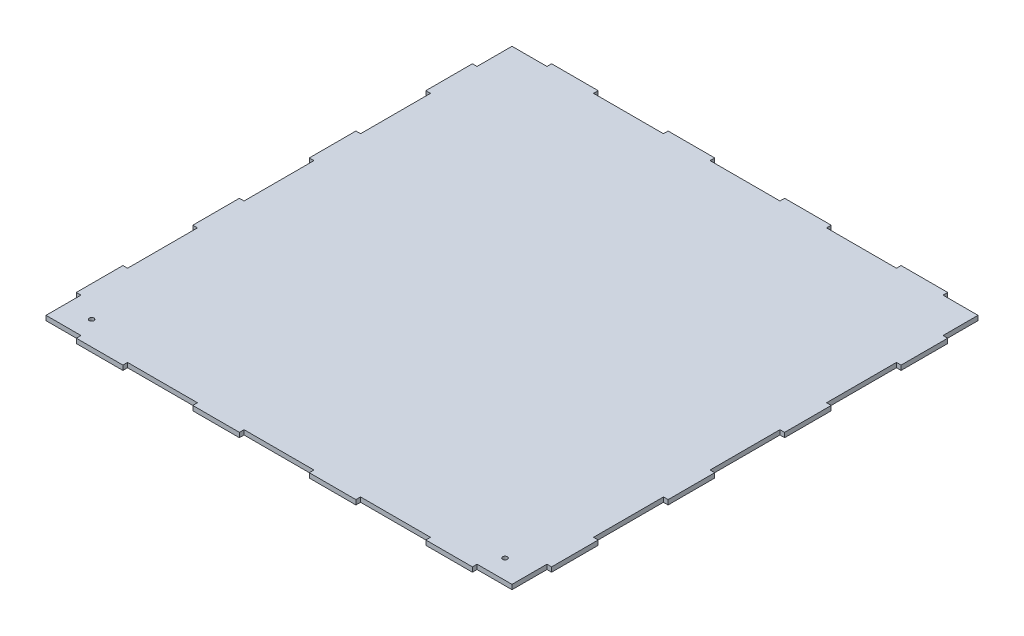
SolidWorks part; units mm, degrees
ref_plane "Front Plane" through (0, 0, 0) normal (0, 0, 1) x (1, 0, 0)
ref_plane "Top Plane" through (0, 0, 0) normal (0, 1, 0) x (1, 0, 0)
ref_plane "Right Plane" through (0, 0, 0) normal (1, 0, 0) x (0, 0, -1)
sketch "Sketch1" plane through (0, 0, 0) normal (0, 1, 0) x (1, 0, 0)
  line L0 (340, 408) -> (260, 408)
  line L1 (400, -400) -> (340, -400)
  line L2 (400, -400) -> (400, -340)
  line L3 (400, 400) -> (340, 400)
  line L4 (-400, -400) -> (-400, -340)
  line L5 (400, -400) -> (-400, 400) construction
  line L6 (400, 400) -> (-400, -400) construction
  line L7 (-408, -340) -> (-408, -260)
  line L8 (340, -408) -> (260, -408)
  line L9 (408, -340) -> (408, -260)
  line L10 (0, 0) -> (0, 601.3427) construction
  line L11 (-200, 601.3427) -> (-200, 42.3001) construction
  line L12 (-300, 493.4621) -> (-300, 335.7003) construction
  line L13 (-340, 408) -> (-340, 400)
  line L14 (-260, 408) -> (-260, 400)
  line L15 (-140, 408) -> (-140, 400)
  line L16 (-60, 408) -> (-60, 400)
  line L17 (60, 408) -> (60, 400)
  line L18 (140, 408) -> (140, 400)
  line L19 (260, 408) -> (260, 400)
  line L20 (340, 408) -> (340, 400)
  line L21 (0, 0) -> (-686.2034, 0) construction
  line L22 (340, -408) -> (340, -400)
  line L23 (260, -408) -> (260, -400)
  line L24 (140, -408) -> (140, -400)
  line L25 (60, -408) -> (60, -400)
  line L26 (-60, -408) -> (-60, -400)
  line L27 (-140, -408) -> (-140, -400)
  line L28 (-260, -408) -> (-260, -400)
  line L29 (-340, -408) -> (-340, -400)
  line L30 (-658.4621, 200) -> (0, 200) construction
  line L31 (-624.1131, 300) -> (-238.3467, 300) construction
  line L32 (-408, 340) -> (-400, 340)
  line L33 (-408, 260) -> (-400, 260)
  line L34 (-408, 140) -> (-400, 140)
  line L35 (-408, 60) -> (-400, 60)
  line L36 (-408, -60) -> (-400, -60)
  line L37 (-408, -140) -> (-400, -140)
  line L38 (-408, -260) -> (-400, -260)
  line L39 (-408, -340) -> (-400, -340)
  line L40 (408, -340) -> (400, -340)
  line L41 (408, -260) -> (400, -260)
  line L42 (408, -140) -> (400, -140)
  line L43 (408, -60) -> (400, -60)
  line L44 (408, 60) -> (400, 60)
  line L45 (408, 140) -> (400, 140)
  line L46 (408, 260) -> (400, 260)
  line L47 (408, 340) -> (400, 340)
  line L48 (-260, 408) -> (-340, 408)
  line L49 (408, 408) -> (-408, 408) construction
  line L50 (-60, 408) -> (-140, 408)
  line L51 (-408, -408) -> (-408, 408) construction
  line L52 (140, 408) -> (60, 408)
  line L53 (408, 260) -> (408, 340)
  line L54 (408, -408) -> (408, 408) construction
  line L55 (408, 60) -> (408, 140)
  line L56 (408, -140) -> (408, -60)
  line L57 (140, -408) -> (60, -408)
  line L58 (408, -408) -> (-408, -408) construction
  line L59 (-60, -408) -> (-140, -408)
  line L60 (-260, -408) -> (-340, -408)
  line L61 (-408, -140) -> (-408, -60)
  line L62 (-408, 60) -> (-408, 140)
  line L63 (-408, 260) -> (-408, 340)
  line L64 (-340, 400) -> (-400, 400)
  line L65 (-140, 400) -> (-260, 400)
  line L66 (400, 400) -> (-400, 400) construction
  line L67 (60, 400) -> (-60, 400)
  line L68 (260, 400) -> (140, 400)
  line L69 (400, 340) -> (400, 400)
  line L70 (400, 140) -> (400, 260)
  line L71 (400, -400) -> (400, 400) construction
  line L72 (400, -60) -> (400, 60)
  line L73 (400, -260) -> (400, -140)
  line L74 (260, -400) -> (140, -400)
  line L75 (60, -400) -> (-60, -400)
  line L76 (400, -400) -> (-400, -400) construction
  line L77 (-140, -400) -> (-260, -400)
  line L78 (-400, -260) -> (-400, -140)
  line L79 (-340, -400) -> (-400, -400)
  line L80 (-400, -400) -> (-400, 400) construction
  line L81 (-400, -60) -> (-400, 60)
  line L82 (-400, 140) -> (-400, 260)
  line L83 (-400, 340) -> (-400, 400)
  point P0 (0, 0)
  dimension "D1" = 800
  dimension "D2" = 800
  dimension "D4" = 200
  dimension "D5" = 100
  dimension "D6" = 40
  dimension "D7" = 200
  dimension "D8" = 100
  dimension "D9" = 40
  dimension "D3" = 8
extrude "Boss-Extrude1" add sketch "Sketch1" along normal blind 8
sketch "Sketch2" plane through (0, 8, 0) normal (0, 1, 0) x (1, 0, 0)
  line L0 (0, 0) -> (0, -487.3791) construction
  line L1 (260, -408) -> (340, -408) construction
  line L2 (408, -340) -> (408, -260) construction
  circle A0 centre (354.85, -366.85) radius 4
  circle A1 centre (-354.85, -366.85) radius 4
  point P9 (451.8421, -412.5776)
  dimension "D1" = 8
  dimension "D2" = 41.15
  dimension "D3" = 53.15
extrude "Cut-Extrude1" cut sketch "Sketch2" against normal blind 10 contours A1 | A0
